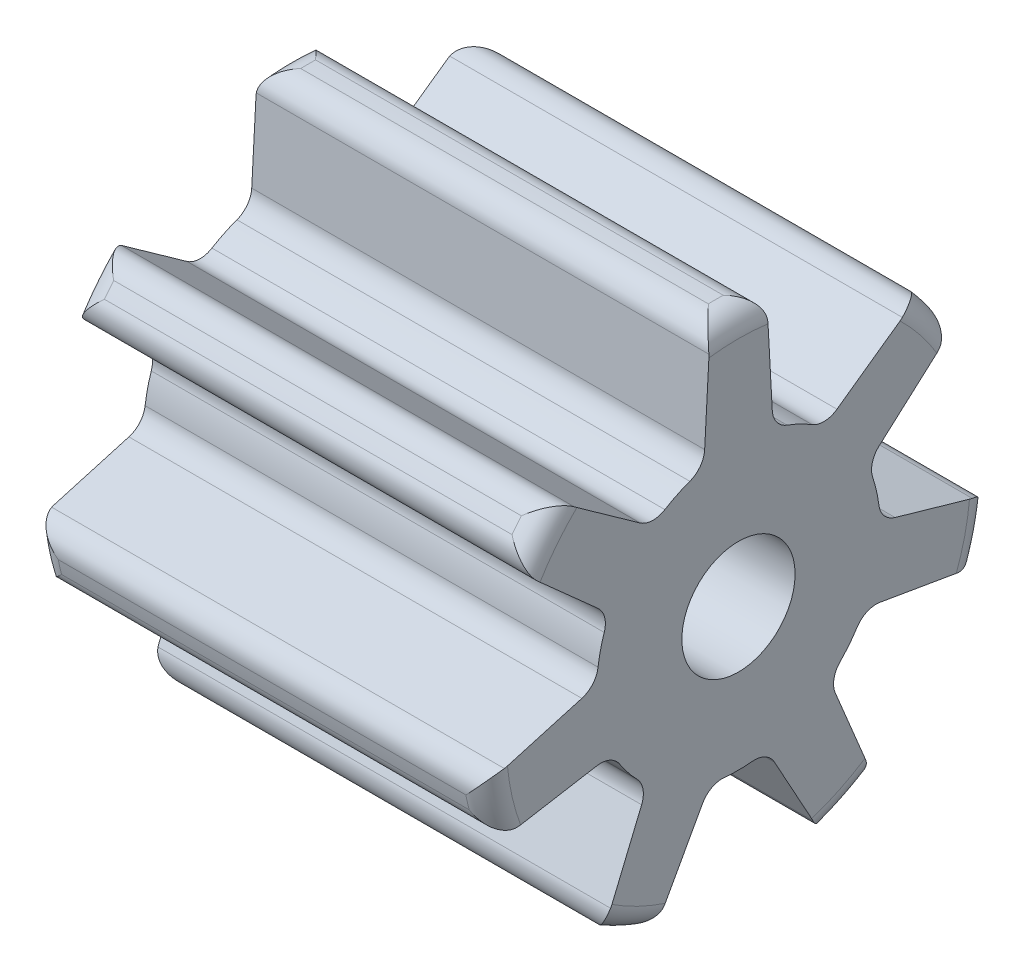
SolidWorks part; units mm, degrees
ref_plane "Front Plane" through (0, 0, 0) normal (0, 0, 1) x (1, 0, 0)
ref_plane "Top Plane" through (0, 0, 0) normal (0, 1, 0) x (1, 0, 0)
ref_plane "Right Plane" through (0, 0, 0) normal (1, 0, 0) x (0, 0, -1)
sketch "Sketch3" plane through (0, 0, 0) normal (1, 0, 0) x (0, 0, -1)
  circle A0 centre (0, 0) radius 2.25
  circle A1 centre (0, 0) radius 0.5
  dimension "D1" = 4.5
  dimension "D2" = 1
extrude "Boss-Extrude1" add sketch "Sketch3" along normal mid plane 4
sketch "Sketch4" plane through (0, 0, 0) normal (1, 0, 0) x (0, 0, -1)
  line L0 (2.2356, -0.2538) -> (1.3833, -0.0095)
  line L1 (0, 0) -> (2.581, 0) construction
  line L2 (1.9041, 1.1987) -> (1.2422, 0.6088)
  line L3 (1.1954, -1.9062) -> (0.8551, -1.0875)
  line L4 (2.1244, -0.7413) -> (1.2505, -0.5916)
  line L5 (-0.745, -2.1231) -> (-0.3171, -1.3465)
  line L6 (0.745, -2.1231) -> (0.3171, -1.3465)
  line L7 (-2.1244, -0.7413) -> (-1.2505, -0.5916)
  line L8 (-1.1954, -1.9062) -> (-0.8551, -1.0875)
  line L9 (-1.9041, 1.1987) -> (-1.2422, 0.6088)
  line L10 (-2.2356, -0.2538) -> (-1.3833, -0.0095)
  line L11 (-0.25, 2.2361) -> (-0.2985, 1.3508)
  line L12 (-1.5924, 1.5896) -> (-0.8699, 1.0756)
  line L16 (0.25, 2.2361) -> (0.2985, 1.3508)
  line L17 (1.5924, 1.5896) -> (0.8699, 1.0756)
  arc A0 (0.65, 1.0677) -> (0.4295, 1.1739) centre (0, 0) ccw
  arc A3 (0.65, 1.0677) -> (0.8699, 1.0756) centre (0.754, 1.2386) ccw
  arc A4 (1.5924, 1.5896) -> (0.25, 2.2361) centre (0, 0) ccw
  arc A5 (0.4295, 1.1739) -> (0.2985, 1.3508) centre (0.4982, 1.3617) cw
  arc A6 (1.24, 0.1575) -> (1.3833, -0.0095) centre (1.4384, 0.1827) ccw
  arc A7 (1.24, 0.1575) -> (1.1856, 0.3961) centre (0, 0) ccw
  arc A8 (2.2356, -0.2538) -> (1.9041, 1.1987) centre (0, 0) ccw
  arc A9 (1.1856, 0.3961) -> (1.2422, 0.6088) centre (1.3753, 0.4595) cw
  arc A10 (0.8963, -0.8713) -> (0.8551, -1.0875) centre (1.0397, -1.0107) ccw
  arc A11 (0.8963, -0.8713) -> (1.0489, -0.68) centre (0, 0) ccw
  arc A12 (1.1954, -1.9062) -> (2.1244, -0.7413) centre (0, 0) ccw
  arc A13 (1.0489, -0.68) -> (1.2505, -0.5916) centre (1.2167, -0.7888) cw
  arc A14 (-0.1223, -1.244) -> (-0.3171, -1.3465) centre (-0.1419, -1.443) ccw
  arc A15 (-0.1223, -1.244) -> (0.1223, -1.244) centre (0, 0) ccw
  arc A16 (-0.745, -2.1231) -> (0.745, -2.1231) centre (0, 0) ccw
  arc A17 (0.1223, -1.244) -> (0.3171, -1.3465) centre (0.1419, -1.443) cw
  arc A18 (-1.0489, -0.68) -> (-1.2505, -0.5916) centre (-1.2167, -0.7888) ccw
  arc A19 (-1.0489, -0.68) -> (-0.8963, -0.8713) centre (0, 0) ccw
  arc A20 (-2.1244, -0.7413) -> (-1.1954, -1.9062) centre (0, 0) ccw
  arc A21 (-0.8963, -0.8713) -> (-0.8551, -1.0875) centre (-1.0397, -1.0107) cw
  arc A22 (-1.1856, 0.3961) -> (-1.2422, 0.6088) centre (-1.3753, 0.4595) ccw
  arc A23 (-1.1856, 0.3961) -> (-1.24, 0.1575) centre (0, 0) ccw
  arc A24 (-1.9041, 1.1987) -> (-2.2356, -0.2538) centre (0, 0) ccw
  arc A25 (-1.24, 0.1575) -> (-1.3833, -0.0095) centre (-1.4384, 0.1827) cw
  arc A26 (-0.4295, 1.1739) -> (-0.2985, 1.3508) centre (-0.4982, 1.3617) ccw
  arc A27 (-0.4295, 1.1739) -> (-0.65, 1.0677) centre (0, 0) ccw
  arc A28 (-0.25, 2.2361) -> (-1.5924, 1.5896) centre (0, 0) ccw
  arc A29 (-0.65, 1.0677) -> (-0.8699, 1.0756) centre (-0.754, 1.2386) cw
  point P9 (0.7566, 0.995)
  point P13 (0.3062, 1.2119)
  dimension "D1" = 2.5
  dimension "D2" = 2.25
  dimension "D3" = 35.433
  dimension "D7" = 0.2
  dimension "D4" = 57.705
  dimension "D5" = 1.0257
  dimension "D6" = 0.5
  dimension "D8" = 7
extrude "Cut-Extrude2" cut sketch "Sketch4" against normal mid plane 4
fillet "Fillet1" radius 0.2 28 edges at (0, -0.7413, -2.1244) (2, -0.5007, -2.1936) (0, -0.2538, -2.2356) (-2, -0.5007, -2.1936) (0, -2.1231, -0.745) (2, -2.0272, -0.9762) (0, -1.9062, -1.1954) (-2, -2.0272, -0.9762) (0, -1.9062, 1.1954) (2, -2.0272, 0.9762) (0, -2.1231, 0.745) (-2, -2.0272, 0.9762) (0, -0.2538, 2.2356) (2, -0.5007, 2.1936) (0, -0.7413, 2.1244) (-2, -0.5007, 2.1936) (0, 1.1987, 1.9041) (-2, 1.4029, 1.7591) (0, 1.5896, 1.5924) (2, 1.4029, 1.7591) (0, 2.2361, -0.25) (2, 2.25, 0) (0, 2.2361, 0.25) (-2, 2.25, 0) (0, 1.5896, -1.5924) (-2, 1.4029, -1.7591) (0, 1.1987, -1.9041) (2, 1.4029, -1.7591)
